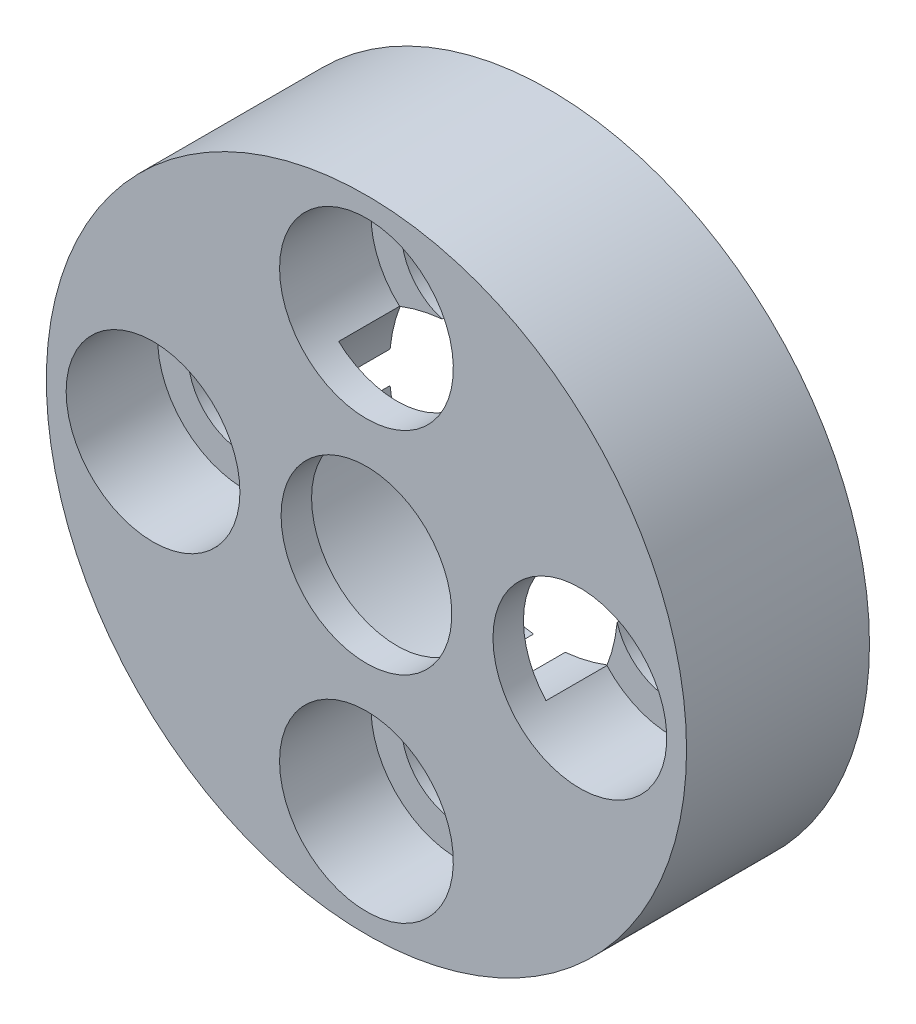
SolidWorks part; units mm, degrees
ref_plane "Front Plane" through (0, 0, 0) normal (0, 0, 1) x (1, 0, 0)
ref_plane "Top Plane" through (0, 0, 0) normal (0, 1, 0) x (1, 0, 0)
ref_plane "Right Plane" through (0, 0, 0) normal (1, 0, 0) x (0, 0, -1)
sketch "Sketch1" plane through (0, 0, 0) normal (0, 0, 1) x (1, 0, 0)
  line L0 (0, 0) -> (50000, 0) construction
  line L1 (0, 0) -> (0, -50000) construction
  circle A0 centre (7, 0) radius 1.85
  circle A1 centre (0, -7) radius 1.85
  circle A3 centre (-7, 0) radius 1.85
  circle A8 centre (0, 7) radius 1.85
  circle A9 centre (0, 0) radius 10.5
  point P1 (8.6412, -4.966)
  point P2 (0, 0)
  point P4 (0, 0)
  point P17 (0, 0)
  dimension "D1" = 3.7
  dimension "D2" = 21
  dimension "D3" = 14
  dimension "D4" = 4
extrude "Boss-Extrude1" add sketch "Sketch1" along normal blind 6
sketch "Sketch2" plane through (0, 0, 0) normal (0, 0, -1) x (-1, 0, 0)
  circle A1 centre (0, 0) radius 5.25
  dimension "D1" = 10.5
extrude "Cut-Extrude1" cut sketch "Sketch2" against normal offset from surface (5 mm away) 1 up to face at (1.85, 7, 6)
sketch "Sketch3" plane through (0, 0, 5) normal (0, 0, -1) x (-1, 0, 0)
  circle A0 centre (0, 0) radius 2.8
  dimension "D1" = 5.6
extrude "Cut-Extrude2" cut sketch "Sketch3" against normal through all
sketch "Sketch5" plane through (0, 0, 6) normal (0, 0, -1) x (-1, 0, 0)
  circle A1 centre (-7, 0) radius 1.85 construction
  circle A3 centre (0, 7) radius 1.85 construction
  circle A5 centre (-7, 0) radius 1.85
  circle A7 centre (0, 7) radius 1.85
  circle A11 centre (0, 7) radius 2.85
  circle A12 centre (7, 0) radius 2.85
  circle A13 centre (0, -7) radius 2.85
  circle A14 centre (-7, 0) radius 2.85
  point P0 (0, 0)
  point P15 (0, 0)
  dimension "D1" = 1
  dimension "D2" = 4
extrude "Cut-Extrude4" cut sketch "Sketch5" along normal offset from surface (3 mm away) 3 up to face at (10.5, 0, 0)
